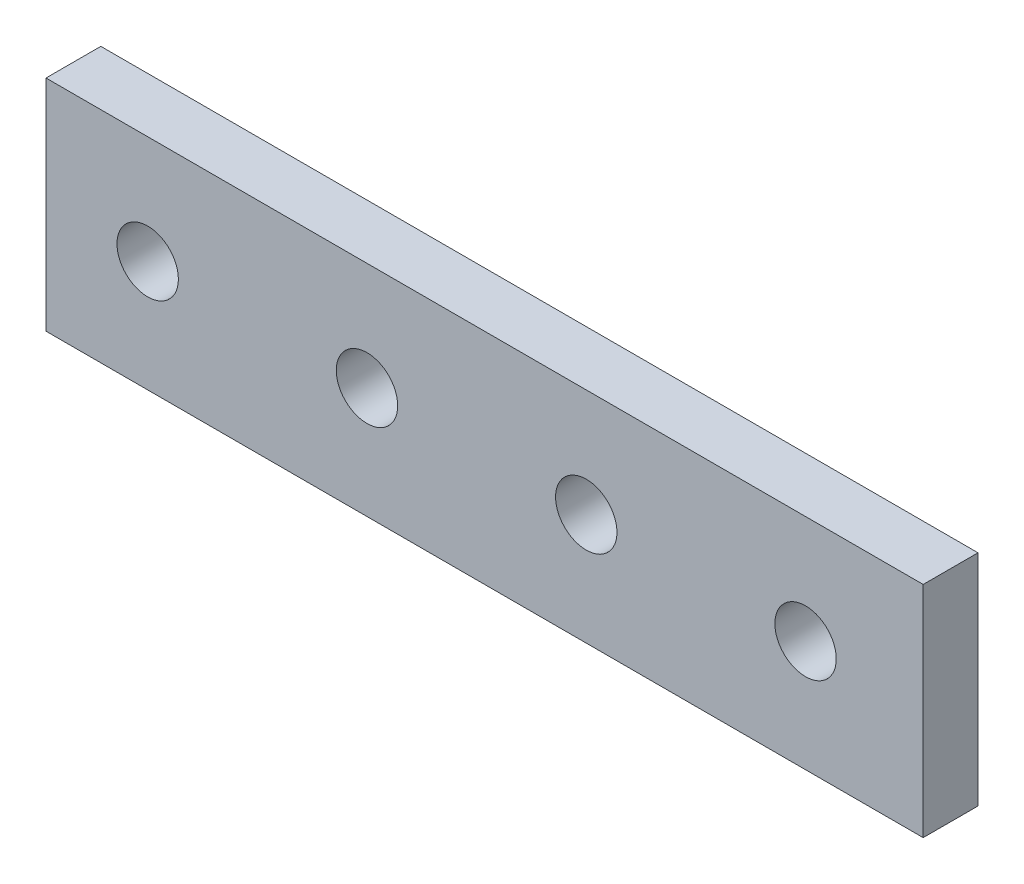
SolidWorks part; units mm, degrees
ref_plane "Front" through (0, 0, 0) normal (0, 0, 1) x (1, 0, 0)
ref_plane "Top" through (0, 0, 0) normal (0, 1, 0) x (1, 0, 0)
ref_plane "Right" through (0, 0, 0) normal (1, 0, 0) x (0, 0, -1)
sketch "Sketch1" plane through (0, 0, 0) normal (0, 0, 1) x (1, 0, 0)
  line L1 (-67.1744, 3.444) -> (34.4256, 3.444)
  line L2 (-67.1744, 3.444) -> (-67.1744, -21.956)
  line L3 (-67.1744, -21.956) -> (34.4256, -21.956)
  line L4 (34.4256, 3.444) -> (34.4256, -21.956)
extrude "Boss-Extrude1" add sketch "Sketch1" along normal blind 6.35
sketch "Sketch2" plane through (0, 0, 6.35) normal (0, 0, 1) x (1, 0, 0)
  line L0 (-55.398, -9.0674) -> (-29.998, -9.0674) construction
  circle A0 centre (-55.398, -9.0674) radius 3.556
  circle A1 centre (-29.998, -9.0674) radius 3.556
  circle A2 centre (-4.598, -9.0674) radius 3.556
  circle A3 centre (20.802, -9.0674) radius 3.556
  dimension "D1" = 25.4
  dimension "D2" = 4
extrude "Cut-Extrude1" cut sketch "Sketch2" against normal through all
